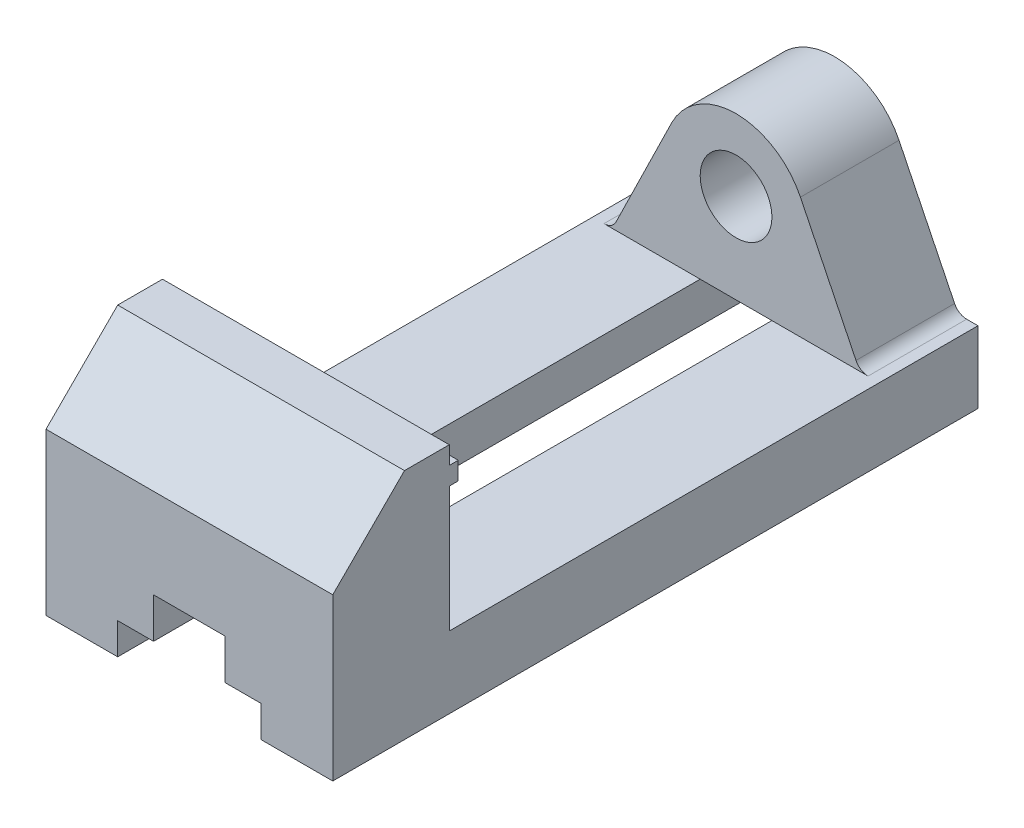
SolidWorks part; units mm, degrees
ref_plane "Front Plane" through (0, 0, 0) normal (0, 0, 1) x (1, 0, 0)
ref_plane "Top Plane" through (0, 0, 0) normal (0, 1, 0) x (1, 0, 0)
ref_plane "Right Plane" through (0, 0, 0) normal (1, 0, 0) x (0, 0, -1)
sketch "Sketch1" plane through (0, 0, 0) normal (1, 0, 0) x (0, 0, -1)
  line L0 (0, 0) -> (0, 36)
  line L1 (0, 36) -> (16, 52)
  line L2 (16, 52) -> (26, 52)
  line L3 (26, 52) -> (26, 16)
  line L4 (26, 16) -> (122, 16)
  line L5 (122, 16) -> (122, 52)
  line L6 (122, 52) -> (144, 52)
  line L7 (144, 52) -> (144, 0)
  line L8 (144, 0) -> (0, 0)
  dimension "D1" = 144
  dimension "D2" = 16
  dimension "D3" = 52
  dimension "D4" = 10
  dimension "D5" = 16
  dimension "D6" = 36
  dimension "D7" = 22
extrude "Boss-Extrude1" add sketch "Sketch1" along normal mid plane 64
sketch "Sketch2" plane through (0, 0, 0) normal (0, 1, 0) x (1, 0, 0)
  line L0 (0, -12.7078) -> (0, 169.6179) construction
  line L1 (47.9554, 0) -> (-47.5485, 0) construction
  line L2 (-32, 144) -> (-22, 144) construction
  line L4 (32, 144) -> (-32, 144) construction
  line L5 (32, 144) -> (22, 144) construction
  line L6 (-32, 0) -> (-22, 0) construction
  line L7 (32, 0) -> (22, 0) construction
  line L8 (-22, 144) -> (-22, 0) construction
  line L9 (22, 144) -> (22, 0) construction
  circle A0 centre (-22, 36) radius 3
  circle A1 centre (22, 36) radius 3
  circle A2 centre (-22, 106) radius 3
  circle A3 centre (22, 106) radius 3
  dimension "D3" = 6
  dimension "D4" = 6
  dimension "D5" = 6
  dimension "D6" = 6
  dimension "D1" = 10
  dimension "D2" = 10
  dimension "D7" = 70
  dimension "D8" = 10
extrude "Cut-Extrude1" cut sketch "Sketch2" along normal blind 10
chamfer "Chamfer2" distance 3 angle 45 1 edges at (22, 10, -103)
chamfer "Chamfer3" distance 3 angle 45 1 edges at (-22, 10, -103)
chamfer "Chamfer4" distance 3 angle 45 1 edges at (22, 10, -33)
chamfer "Chamfer5" distance 3 angle 45 1 edges at (-22, 10, -33)
sketch "Sketch6" plane through (0, 0, 0) normal (0, 0, 1) x (1, 0, 0)
  line L0 (0, 0) -> (0, 16.609) construction
  line L1 (32, 0) -> (-32, 0) construction
  line L2 (0, 0) -> (-16, 0) construction
  line L3 (-16, 0) -> (-16, 7)
  line L4 (-16, 7) -> (-8, 7)
  line L5 (-8, 7) -> (-8, 16)
  line L6 (-8, 16) -> (0, 16)
  line L7 (0, 16) -> (8, 16)
  line L8 (8, 16) -> (8, 7)
  line L9 (8, 7) -> (16, 7)
  line L10 (16, 7) -> (16, 0)
  line L11 (-16, 0) -> (16, 0)
  dimension "D1" = 32
  dimension "D2" = 8
  dimension "D3" = 8
  dimension "D4" = 8
  dimension "D5" = 7
  dimension "D6" = 16
extrude "Cut-Extrude3" cut sketch "Sketch6" against normal through all
sketch "Sketch7" plane through (0, 0, -144) normal (0, 0, -1) x (-1, 0, 0)
  line L0 (0, 0) -> (0, 53.6484) construction
  circle A0 centre (0, 36) radius 8
  dimension "D1" = 16
  dimension "D2" = 36
extrude "Cut-Extrude4" cut sketch "Sketch7" against normal up to next
sketch "Sketch8" plane through (0, 0, -144) normal (0, 0, -1) x (-1, 0, 0)
  line L0 (-32, 0) -> (-32, 7)
  line L1 (-32, 0) -> (-32, 52) construction
  line L2 (32, 0) -> (32, 7)
  line L3 (32, 0) -> (32, 52) construction
  line L4 (0, 0) -> (0, 59.1112) construction
  line L5 (32, 7) -> (14.3722, 43.0314)
  line L6 (-32, 7) -> (-14.3722, 43.0314)
  line L7 (-32, 0) -> (32, 0)
  line L8 (-32, 7) -> (-32, 52)
  line L9 (-32, 52) -> (32, 52) construction
  line L10 (-32, 52) -> (32, 52)
  line L11 (32, 52) -> (32, 7)
  line L12 (32, 16) -> (-32, 16)
  arc A0 (14.3722, 43.0314) -> (-14.3722, 43.0314) centre (0, 36) ccw
  circle A1 centre (0, 36) radius 8 construction
  line M11 (32, 52) -> (-32, 52)
  line M12 (-32, 52) -> (-32, 0)
  dimension "D1" = 7
  dimension "D2" = 16
extrude "Cut-Extrude8" cut sketch "Sketch8" against normal up to next contours A0 L10 L12 L6 M12 | A0 L5 L12 L11 M11
fillet "Fillet1" radius 3 2 edges at (27.5969, 16, -133) (-27.5969, 16, -133)
sketch "Sketch9" plane through (0, 0, -26) normal (0, 0, -1) x (-1, 0, 0)
  line L0 (-32, 16) -> (-32, 52) construction
  line L1 (-32, 48) -> (32, 48)
  line L2 (-32, 48) -> (-32, 44)
  line L3 (-32, 44) -> (32, 44)
  line L4 (32, 48) -> (32, 44)
  line L5 (32, 16) -> (32, 52) construction
  line L6 (-32, 52) -> (32, 52) construction
  dimension "D1" = 4
  dimension "D2" = 4
extrude "Boss-Extrude2" add sketch "Sketch9" along normal blind 2
